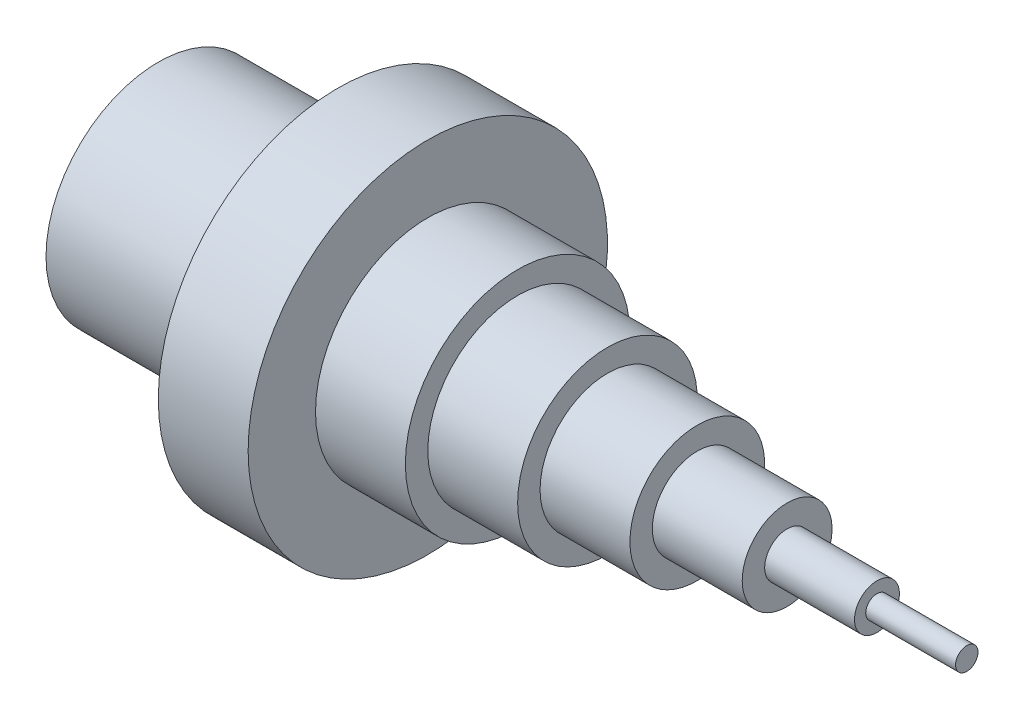
SolidWorks part; units mm, degrees
ref_plane "Front Plane" through (0, 0, 0) normal (0, 0, 1) x (1, 0, 0)
ref_plane "Top Plane" through (0, 0, 0) normal (0, 1, 0) x (1, 0, 0)
ref_plane "Right Plane" through (0, 0, 0) normal (1, 0, 0) x (0, 0, -1)
sketch "Sketch1" plane through (0, 0, 0) normal (0, 0, 1) x (1, 0, 0)
  line L0 (0, 0) -> (180, 0) construction
  line L1 (0, 0) -> (0, -25)
  line L2 (0, -25) -> (40, -25)
  line L3 (40, -25) -> (40, -40)
  line L4 (40, -40) -> (60, -40)
  line L5 (60, -40) -> (60, -25)
  line L6 (60, -25) -> (80, -25)
  line L7 (80, -25) -> (80, -20)
  line L8 (80, -20) -> (100, -20)
  line L9 (100, -20) -> (100, -15)
  line L10 (100, -15) -> (120, -15)
  line L11 (120, -15) -> (120, -10)
  line L12 (120, -10) -> (140, -10)
  line L13 (140, -10) -> (140, -5)
  line L14 (140, -5) -> (160, -5)
  line L15 (160, -5) -> (160, -2.5)
  line L16 (160, -2.5) -> (180, -2.5)
  line L17 (180, 0) -> (180, -2.5)
  line L18 (0, 0) -> (180, 0)
  dimension "D1" = 50
  dimension "D7" = 20
  dimension "D2" = 80
  dimension "D3" = 50
  dimension "D4" = 40
  dimension "D5" = 30
  dimension "D6" = 20
  dimension "D8" = 20
  dimension "D9" = 40
  dimension "D10" = 20
  dimension "D11" = 20
  dimension "D12" = 20
  dimension "D13" = 20
  dimension "D14" = 20
  dimension "D15" = 10
  dimension "D16" = 5
revolve "Revolve1" add sketch "Sketch1" angle 360 about L0
sketch "Sketch2" plane through (0, 0, 0) normal (-1, 0, 0) x (0, 0, 1)
  circle A0 centre (0, 0) radius 20
  point P3 (7.3906, -9.6538)
extrude "Cut-Extrude1" cut sketch "Sketch2" against normal blind 40
